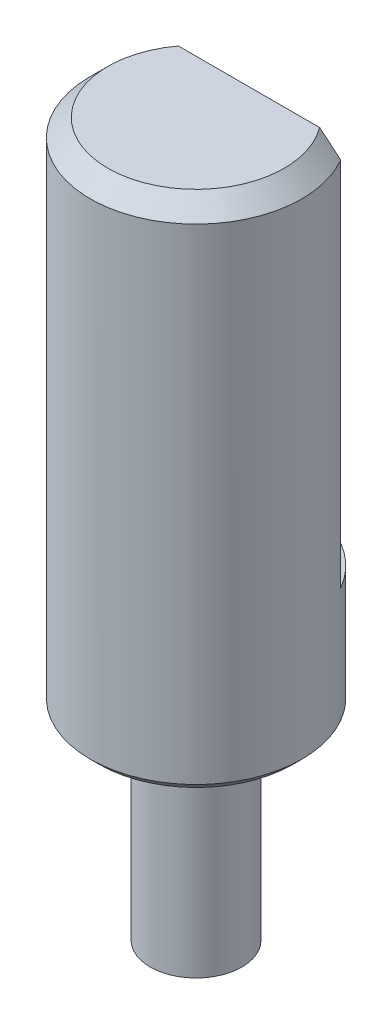
SolidWorks part; units mm, degrees
ref_plane "Front" through (0, 0, 0) normal (0, 0, 1) x (1, 0, 0)
ref_plane "Top" through (0, 0, 0) normal (0, 1, 0) x (1, 0, 0)
ref_plane "Right" through (0, 0, 0) normal (1, 0, 0) x (0, 0, -1)
sketch "草图1" plane through (0, 0, 0) normal (0, 1, 0) x (1, 0, 0)
  circle A0 centre (0, 0) radius 1.3
  dimension "D1" = 2.6
extrude "凸台-拉伸1" add sketch "草图1" along normal blind 5.7
sketch "草图2" plane through (0, 5.7, 0) normal (0, 1, 0) x (1, 0, 0)
  circle A0 centre (0, 0) radius 3
  dimension "D1" = 6
extrude "凸台-拉伸2" add sketch "草图2" along normal blind 14.5
chamfer "倒角1" distance 0.25 angle 45 1 edges at (0, 5.7, 3)
sketch "草图3" plane through (0, 20.2, 0) normal (0, 1, 0) x (1, 0, 0)
  line L0 (-2.5981, 1.5) -> (2.5981, 1.5)
  circle A2 centre (0, 0) radius 3
  arc A3 (2.5981, 1.5) -> (-2.5981, 1.5) centre (0, 0) ccw
  dimension "D2" = 1.5
  dimension "D1" = 0
extrude "切除-拉伸1" cut sketch "草图3" against normal blind 11
chamfer "倒角2" distance 0.5 angle 45 1 edges at (0, 20.2, 3)
